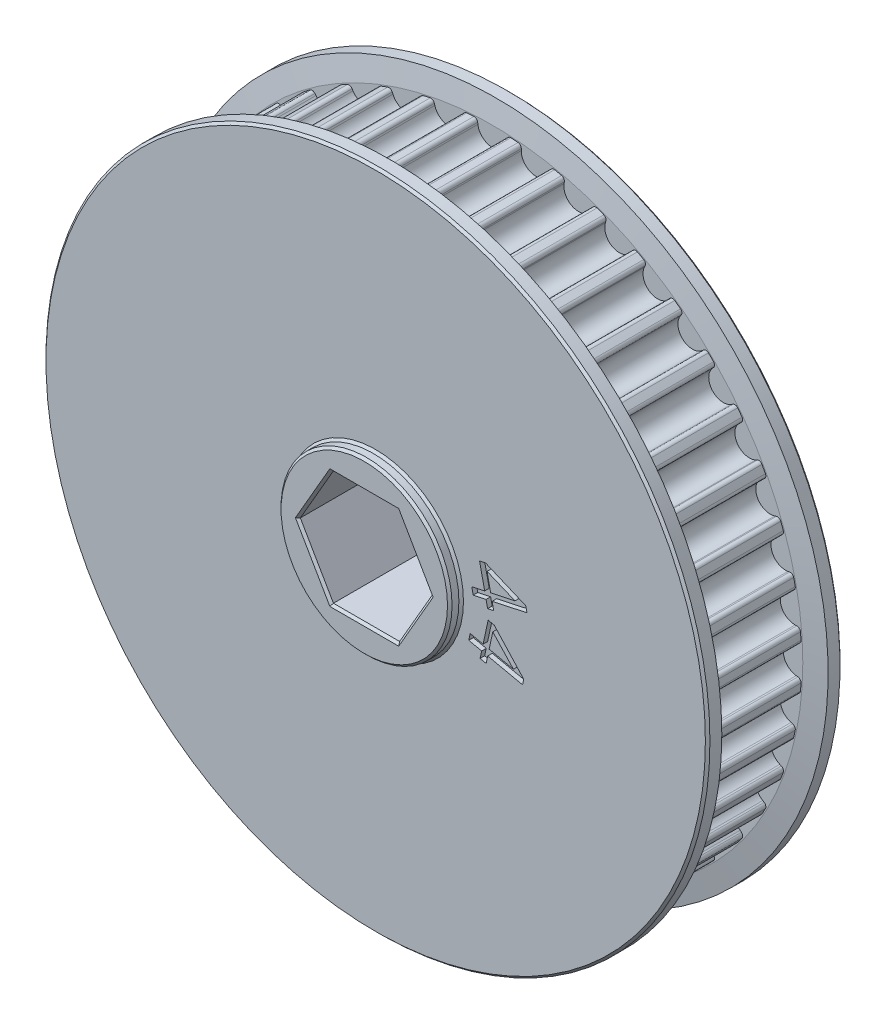
SolidWorks part; units mm, degrees
material "ABS"
ref_plane "Front Plane" through (0, 0, 0) normal (0, 0, 1) x (1, 0, 0)
ref_plane "Top Plane" through (0, 0, 0) normal (0, 1, 0) x (1, 0, 0)
ref_plane "Right Plane" through (0, 0, 0) normal (1, 0, 0) x (0, 0, -1)
sketch "Sketch2" plane through (0, 0, 0) normal (0, 0, 1) x (1, 0, 0)
  circle A0 centre (0, 0) radius 34.4439
extrude "pulley" add sketch "Sketch2" along normal mid plane 11
sketch "tooth" plane through (0, 0, 0) normal (0, 0, 1) x (1, 0, 0)
  line L0 (0, 0) -> (0, 34.0439) construction
  line L1 (4.9865, 33.6767) -> (0, 34.0439) construction
  line L2 (4.9865, 33.6767) -> (0, 0) construction
  line L3 (-2.1327, 38.0794) -> (-1.6129, 33.8458)
  line L6 (2.1327, 38.0794) -> (1.6129, 33.8458)
  line L7 (-2.1327, 38.0794) -> (2.1327, 38.0794)
  arc A1 (-1.6129, 33.8458) -> (1.6129, 33.8458) centre (0, 34.0439) ccw
  arc A2 (0, 34.0439) -> (4.9865, 33.6767) centre (0, 0) cw construction
  circle A3 centre (4.9865, 33.6767) radius 1.625 construction
extrude "cut tooth" cut sketch "tooth" against normal mid plane 11
fillet "blend tooth" radius 0.4 2 edges at (1.6813, 34.4028, 0) (-1.6813, 34.4028, 0)
pattern_circular "tooth pattern" count 44 over 360 about axis through (0, 0, 0) along (0, 0, 1) of "cut tooth", "blend tooth"
sketch "Sketch3" plane through (0, 0, 0) normal (0, 0, 1) x (1, 0, 0)
  circle A0 centre (0, 0) radius 36.9839
  circle A1 centre (0, 0) radius 34.4439 construction
  dimension "D1" = 2.54
extrude "sidewall" add sketch "Sketch3" along normal blind 2 from offset 5.5
mirror "mirror sidewall" about plane through (0, 0, 0) normal (0, 0, 1) of "sidewall"
chamfer "sidewall chamfer" distance 2.4 angle 10 2 edges at (36.9839, 0, 5.5) (36.9839, 0, -5.5)
sketch "Sketch5" plane through (0, 0, 0) normal (0, 0, 1) x (1, 0, 0)
  circle A0 centre (0, 0) radius 9.525
  dimension "D1" = 19.05
extrude "bearing spacer (Manual Suppress)" add sketch "Sketch5" along normal blind 8.77 and the other way blind 8.77
sketch "Sketch4" plane through (0, 0, 0) normal (0, 0, 1) x (1, 0, 0)
  line L1 (3.6882, 6.3881) -> (-3.6882, 6.3881)
  line L2 (-3.6882, 6.3881) -> (-7.3763, 0)
  line L3 (-7.3763, 0) -> (-3.6882, -6.3881)
  line L4 (-3.6882, -6.3881) -> (3.6882, -6.3881)
  line L5 (3.6882, -6.3881) -> (7.3763, 0)
  line L6 (7.3763, 0) -> (3.6882, 6.3881)
  circle A0 centre (0, 0) radius 6.3881 construction
  dimension "D1" = 12.7762
extrude "hex shaft" cut sketch "Sketch4" against normal mid plane 127
chamfer "chamfers" distance 0.254 angle 45 18 edges at (36.9839, 0, -7.5) (36.9839, 0, 7.5) (-9.525, 0, -7.5) (9.525, 0, 7.5) (9.525, 0, 8.77) (0, 6.3881, 8.77) (-5.5323, 3.194, 8.77) (-5.5323, -3.194, 8.77) (0, -6.3881, 8.77) (5.5323, -3.194, 8.77) (5.5323, 3.1941, 8.77) (9.525, 0, -8.77) (0, -6.3881, -8.77) (-5.5323, -3.194, -8.77) (-5.5323, 3.194, -8.77) (0, 6.3881, -8.77) (5.5323, 3.1941, -8.77) (5.5323, -3.194, -8.77)
sketch "SK-VersaCut" plane through (0, 0, 0) normal (0, 0, 1) x (1, 0, 0)
  line B0 (6.3387, 23.6565) -> (5.299, 19.7762)
  line B1 (14.4772, 14.4772) -> (17.3177, 17.3177)
  line B2 (23.6565, 6.3387) -> (19.7762, 5.299)
  line B3 (19.7762, -5.299) -> (23.6565, -6.3387)
  line B4 (17.3177, -17.3177) -> (14.4772, -14.4772)
  line B5 (5.299, -19.7762) -> (6.3387, -23.6565)
  line B6 (-6.3387, -23.6565) -> (-5.299, -19.7762)
  line B7 (-14.4772, -14.4772) -> (-17.3177, -17.3177)
  line B8 (-23.6565, -6.3387) -> (-19.7762, -5.299)
  line B9 (-19.7762, 5.299) -> (-23.6565, 6.3387)
  line B10 (-17.3177, 17.3177) -> (-14.4772, 14.4772)
  line B11 (-5.299, 19.7762) -> (-6.3387, 23.6565)
  circle B12 centre (0, 23.8125) radius 2.2479
  arc B13 (5.9535, 18.5765) -> (13.1109, 14.4442) centre (0, 0) cw
  arc B14 (7.5904, 24.3458) -> (17.2889, 18.7464) centre (0, 0) cw
  arc B15 (5.9535, 18.5765) -> (5.299, 19.7762) centre (6.2559, 19.5198) cw
  arc B16 (13.1109, 14.4442) -> (14.4772, 14.4772) centre (13.7767, 15.1777) ccw
  arc B17 (17.2889, 18.7464) -> (17.3177, 17.3177) centre (16.6173, 18.0182) cw
  arc B18 (7.5904, 24.3458) -> (6.3387, 23.6565) centre (7.2956, 23.4001) ccw
  circle B19 centre (20.6222, 11.9062) radius 2.2479
  arc B20 (19.0645, 4.1323) -> (19.0645, -4.1323) centre (0, 0) cw
  arc B21 (24.8793, 5.5994) -> (24.8793, -5.5994) centre (0, 0) cw
  arc B22 (19.0645, 4.1323) -> (19.7762, 5.299) centre (20.0326, 4.3422) cw
  arc B23 (19.0645, -4.1323) -> (19.7762, -5.299) centre (20.0326, -4.3422) ccw
  arc B24 (24.8793, -5.5994) -> (23.6565, -6.3387) centre (23.9129, -5.3819) cw
  arc B25 (24.8793, 5.5994) -> (23.6565, 6.3387) centre (23.9129, 5.3819) ccw
  circle B26 centre (20.6222, -11.9063) radius 2.2479
  arc B27 (13.1109, -14.4442) -> (5.9535, -18.5765) centre (0, 0) cw
  arc B28 (17.2889, -18.7464) -> (7.5904, -24.3458) centre (0, 0) cw
  arc B29 (13.1109, -14.4442) -> (14.4772, -14.4772) centre (13.7767, -15.1777) cw
  arc B30 (5.9535, -18.5765) -> (5.299, -19.7762) centre (6.2559, -19.5198) ccw
  arc B31 (7.5904, -24.3458) -> (6.3387, -23.6565) centre (7.2956, -23.4001) cw
  arc B32 (17.2889, -18.7464) -> (17.3177, -17.3177) centre (16.6173, -18.0182) ccw
  circle B33 centre (0, -23.8125) radius 2.2479
  arc B34 (-5.9535, -18.5765) -> (-13.1109, -14.4442) centre (0, 0) cw
  arc B35 (-7.5904, -24.3458) -> (-17.2889, -18.7464) centre (0, 0) cw
  arc B36 (-5.9535, -18.5765) -> (-5.299, -19.7762) centre (-6.2559, -19.5198) cw
  arc B37 (-13.1109, -14.4442) -> (-14.4772, -14.4772) centre (-13.7767, -15.1777) ccw
  arc B38 (-17.2889, -18.7464) -> (-17.3177, -17.3177) centre (-16.6173, -18.0182) cw
  arc B39 (-7.5904, -24.3458) -> (-6.3387, -23.6565) centre (-7.2956, -23.4001) ccw
  circle B40 centre (-20.6222, -11.9063) radius 2.2479
  arc B41 (-19.0645, -4.1323) -> (-19.0645, 4.1323) centre (0, 0) cw
  arc B42 (-24.8793, -5.5994) -> (-24.8793, 5.5994) centre (0, 0) cw
  arc B43 (-19.0645, -4.1323) -> (-19.7762, -5.299) centre (-20.0326, -4.3422) cw
  arc B44 (-19.0645, 4.1323) -> (-19.7762, 5.299) centre (-20.0326, 4.3422) ccw
  arc B45 (-24.8793, 5.5994) -> (-23.6565, 6.3387) centre (-23.9129, 5.3819) cw
  arc B46 (-24.8793, -5.5994) -> (-23.6565, -6.3387) centre (-23.9129, -5.3819) ccw
  circle B47 centre (-20.6222, 11.9063) radius 2.2479
  arc B48 (-13.1109, 14.4442) -> (-5.9535, 18.5765) centre (0, 0) cw
  arc B49 (-17.2889, 18.7464) -> (-7.5904, 24.3458) centre (0, 0) cw
  arc B50 (-13.1109, 14.4442) -> (-14.4772, 14.4772) centre (-13.7767, 15.1777) cw
  arc B51 (-5.9535, 18.5765) -> (-5.299, 19.7762) centre (-6.2559, 19.5198) ccw
  arc B52 (-7.5904, 24.3458) -> (-6.3387, 23.6565) centre (-7.2956, 23.4001) cw
  arc B53 (-17.2889, 18.7464) -> (-17.3177, 17.3177) centre (-16.6173, 18.0182) ccw
sketch_block_instance "VersaKey-1"
sketch_block "Block1" parameters "D1"=47.625, "D2"=4.4958, "D3"=19.5072, "D4"=25.5016, "D6"=0.9906, "D5"=30
extrude "VersaKey (Manual Suppress)" [suppressed] cut sketch "SK-VersaCut" against normal through all both and the other way through all
sketch "Lightening Holes" plane through (0, 0, 0) normal (0, 0, 1) x (1, 0, 0)
  line L0 (-11.9573, 25.7906) -> (-3.9521, 11.9253)
  line L1 (3.9521, 11.9253) -> (11.9573, 25.7906)
  line L14 (0, 0) -> (-3.6662, 6.35) construction
  line L15 (0, 0) -> (0, 6.35) construction
  line L24 (0, 0) -> (3.6662, 6.35) construction
  line L25 (0, 6.35) -> (-3.6662, 6.35) construction
  line L26 (0, 6.35) -> (3.6662, 6.35) construction
  line L27 (-3.0943, 11.43) -> (3.0943, 11.43)
  line L28 (0, 6.35) -> (0, 11.43) construction
  line L29 (16.3567, 23.2506) -> (8.3515, 9.3853)
  line L30 (8.3515, 8.3947) -> (11.4458, 3.0353)
  line L31 (12.3037, 2.54) -> (28.314, 2.54)
  line L32 (28.314, -2.54) -> (12.3037, -2.54)
  line L33 (11.4458, -3.0353) -> (8.3515, -8.3947)
  line L34 (8.3515, -9.3853) -> (16.3567, -23.2506)
  line L35 (11.9573, -25.7906) -> (3.9521, -11.9253)
  line L36 (3.0943, -11.43) -> (-3.0943, -11.43)
  line L37 (-3.9521, -11.9253) -> (-11.9573, -25.7906)
  line L38 (-16.3567, -23.2506) -> (-8.3515, -9.3853)
  line L39 (-8.3515, -8.3947) -> (-11.4458, -3.0353)
  line L40 (-12.3037, -2.54) -> (-28.314, -2.54)
  line L41 (-28.314, 2.54) -> (-12.3037, 2.54)
  line L42 (-11.4458, 3.0353) -> (-8.3515, 8.3947)
  line L43 (-8.3515, 9.3853) -> (-16.3567, 23.2506)
  arc A3 (-11.4847, 27.1985) -> (11.4847, 27.1985) centre (0, 0) cw
  arc A4 (-3.0943, 11.43) -> (-3.9521, 11.9253) centre (-3.0943, 12.4206) cw
  arc A5 (3.0943, 11.43) -> (3.9521, 11.9253) centre (3.0943, 12.4206) ccw
  arc A6 (11.4847, 27.1985) -> (11.9573, 25.7906) centre (11.0994, 26.2859) cw
  arc A7 (-11.4847, 27.1985) -> (-11.9573, 25.7906) centre (-11.0994, 26.2859) ccw
  arc A72 (17.8122, 23.5453) -> (29.297, 3.6532) centre (0, 0) cw
  arc A73 (17.8122, 23.5453) -> (16.3567, 23.2506) centre (17.2146, 22.7553) ccw
  arc A74 (8.3515, 8.3947) -> (8.3515, 9.3853) centre (9.2094, 8.89) cw
  arc A75 (29.297, 3.6532) -> (28.314, 2.54) centre (28.314, 3.5306) cw
  arc A76 (29.297, -3.6532) -> (17.8122, -23.5453) centre (0, 0) cw
  arc A77 (29.297, -3.6532) -> (28.314, -2.54) centre (28.314, -3.5306) ccw
  arc A78 (11.4458, -3.0353) -> (12.3037, -2.54) centre (12.3037, -3.5306) cw
  arc A79 (17.8122, -23.5453) -> (16.3567, -23.2506) centre (17.2146, -22.7553) cw
  arc A80 (11.4847, -27.1985) -> (-11.4847, -27.1985) centre (0, 0) cw
  arc A81 (11.4847, -27.1985) -> (11.9573, -25.7906) centre (11.0994, -26.2859) ccw
  arc A82 (3.0943, -11.43) -> (3.9521, -11.9253) centre (3.0943, -12.4206) cw
  arc A83 (-11.4847, -27.1985) -> (-11.9573, -25.7906) centre (-11.0994, -26.2859) cw
  arc A84 (-17.8122, -23.5453) -> (-29.297, -3.6532) centre (0, 0) cw
  arc A85 (-17.8122, -23.5453) -> (-16.3567, -23.2506) centre (-17.2146, -22.7553) ccw
  arc A86 (-8.3515, -8.3947) -> (-8.3515, -9.3853) centre (-9.2094, -8.89) cw
  arc A87 (-29.297, -3.6532) -> (-28.314, -2.54) centre (-28.314, -3.5306) cw
  arc A88 (-29.297, 3.6532) -> (-17.8122, 23.5453) centre (0, 0) cw
  arc A89 (-29.297, 3.6532) -> (-28.314, 2.54) centre (-28.314, 3.5306) ccw
  arc A90 (-11.4458, 3.0353) -> (-12.3037, 2.54) centre (-12.3037, 3.5306) cw
  arc A91 (-17.8122, 23.5453) -> (-16.3567, 23.2506) centre (-17.2146, 22.7553) cw
  arc A92 (11.4458, 3.0353) -> (12.3037, 2.54) centre (12.3037, 3.5306) ccw
  arc A93 (8.3515, -8.3947) -> (8.3515, -9.3853) centre (9.2094, -8.89) ccw
  arc A94 (-3.0943, -11.43) -> (-3.9521, -11.9253) centre (-3.0943, -12.4206) ccw
  arc A95 (-11.4458, -3.0353) -> (-12.3037, -2.54) centre (-12.3037, -3.5306) ccw
  arc A96 (-8.3515, 8.3947) -> (-8.3515, 9.3853) centre (-9.2094, 8.89) ccw
  point P72 (0, 0)
  point P77 (0, 0)
  point P87 (0, 0)
extrude "Lightening Holes (Man Suppress)" [suppressed] cut sketch "Lightening Holes" against normal through all both and the other way through all
sketch "Sketch6" plane through (0, 0, 0) normal (0, 0, 1) x (1, 0, 0)
  line L0 (0, 11.1154) -> (0, 0) construction
  line L1 (0, 0) -> (0, -11.1154) construction
  arc A1 (0, 11.1154) -> (0, -11.1154) centre (0, 0) cw construction
  arc A2 (0, 11.1154) -> (0, -11.1154) centre (0, 0) ccw construction
  text T0 "44\r\n" font "DS-Digital" height in points 24
extrude "4419" cut sketch "Sketch6" along normal blind 2.54 from offset 6.992
sketch "Sketch7" plane through (0, 0, -7.5) normal (0, 0, -1) x (-1, 0, 0)
  circle A0 centre (0, 0) radius 22.225
  circle A1 centre (0, 0) radius 28.575
  dimension "D1" = 44.45
  dimension "D2" = 57.15
extrude "Path for motor's bolts" cut sketch "Sketch7" against normal blind 3.175
equation "\"INPUT_pulley_teeth\"= 44"
equation "\"pulley_c2c\"= 5mm"
equation "\"pulley_teeth_deg\"= 360 / \"INPUT_pulley_teeth\""
equation "\"pulley_radius\"= ( \"pulley_c2c\" / ( 2 * cos ( \"iso_half_angle\" ) ) ) - 1mm"
equation "\"iso_half_angle\"= ( 180 - \"pulley_teeth_deg\" ) / 2"
equation "\"D1@tooth\" = \"pulley_radius\""
equation "\"pulley_tooth_dia\"= 3.25mm"
equation "\"D3@tooth\"=\"pulley_c2c\""
equation "\"D2@tooth\"=\"pulley_tooth_dia\""
equation "\"D1@Sketch2\"=2* \"pulley_radius\"+\"pulley_tooth_offset\""
equation "\"pulley_tooth_offset\"= .8mm"
equation "\"D1@tooth pattern\" = \"INPUT_pulley_teeth\""
equation "\"INPUT_pulley_belt_9_or_15_(unitless)\"= 9"
equation "\"D1@pulley\"=\"pulley_width\""
equation "\"D19@sidewall\" =  ( \"pulley_width\" / 2 ) "
equation "\"D1@sidewall\"=\"pulley_sidewall_thick\""
equation "\"pulley_width\"= IIF ( \"INPUT_pulley_belt_9_or_15_(unitless)\" = 9 , 11mm , 17mm )"
equation "\"D1@cut tooth\"=\"pulley_width\""
equation "\"D1@sidewall chamfer\" = 2.4mm"
equation "\"D4@Lightening Holes\"=\"pulley_radius\"-\"pulley_tooth_dia\"-.05"
equation "\"D1@bearing spacer (Manual Suppress)\" = 0.05 +  ( \"pulley_width\" / 2 )  + \"pulley_sidewall_thick\""
equation "\"D2@bearing spacer (Manual Suppress)\" = 0.05 +  ( \"pulley_width\" / 2 )  + \"pulley_sidewall_thick\""
equation "\"pulley_sidewall_thick\"= 2mm"
equation "\"D1@4419\" = \"pulley_width\""
equation "\"D19@4419\"=(\"pulley_width\" / 2) +\"pulley_sidewall_thick\" - 0.02"
equation "\"rad_len\" = \"INPUT_pulley_teeth\" * \"pulley_c2c\""
